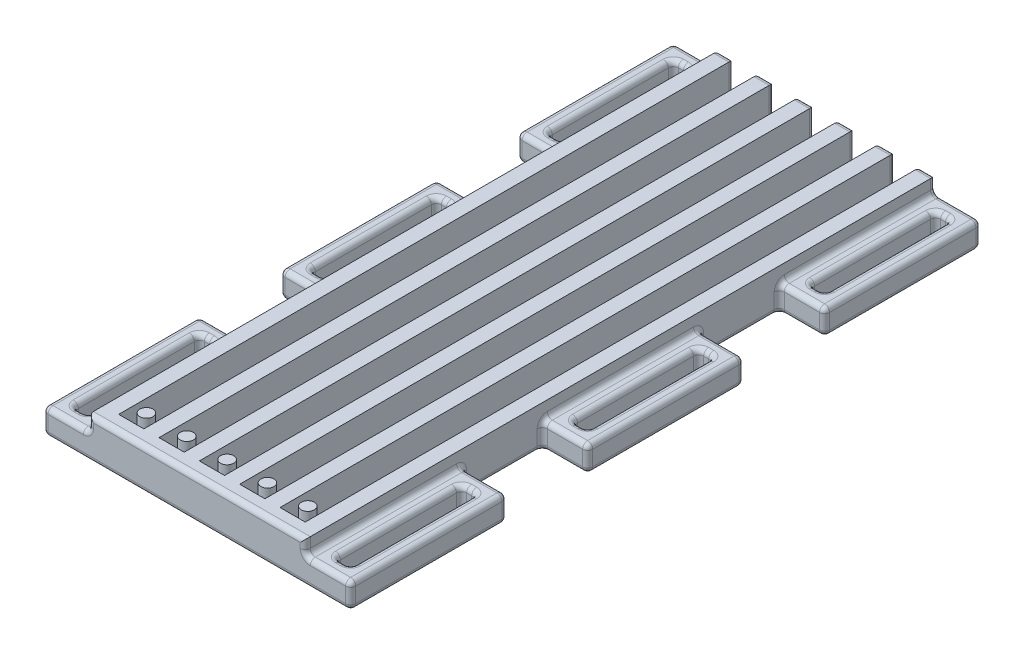
SolidWorks part; units mm, degrees
ref_plane "Front Plane" through (0, 0, 0) normal (0, 0, 1) x (1, 0, 0)
ref_plane "Top Plane" through (0, 0, 0) normal (0, 1, 0) x (1, 0, 0)
ref_plane "Right Plane" through (0, 0, 0) normal (1, 0, 0) x (0, 0, -1)
sketch "Sketch1" plane through (0, 0, 0) normal (0, 1, 0) x (1, 0, 0)
  line L1 (0, 0) -> (43, 0)
  line L2 (0, 0) -> (0, 125)
  line L3 (0, 125) -> (43, 125)
  line L4 (43, 0) -> (43, 125)
extrude "Boss-Extrude2" add sketch "Sketch1" along normal blind 8 contours L3 L4 L1 L2
sketch "Sketch2" plane through (0, 8, 0) normal (0, 1, 0) x (1, 0, 0)
  line L0 (8, 125) -> (8, 3)
  line L1 (3, 3) -> (40, 3)
  line L2 (3, 3) -> (3, 125)
  line L3 (3, 125) -> (40, 125)
  line L4 (40, 3) -> (40, 125)
  line L5 (11, 125) -> (11, 3)
  line L6 (16, 125) -> (16, 3)
  line L7 (19, 125) -> (19, 3)
  line L8 (24, 125) -> (24, 3)
  line L9 (27, 125) -> (27, 3)
  line L10 (32, 125) -> (32, 3)
  line L11 (35, 125) -> (35, 3)
  line L12 (0, 0) -> (0, 125) construction
  line L14 (0, 0) -> (43, 0) construction
  line L15 (0, 125) -> (43, 125) construction
  dimension "D1" = 3
  dimension "D2" = 3
  dimension "D3" = 3
  dimension "D4" = 3
  dimension "D5" = 5
  dimension "D6" = 5
  dimension "D7" = 5
  dimension "D8" = 5
  dimension "D9" = 5
  dimension "D10" = 3
  dimension "D11" = 3
extrude "Cut-Extrude1" cut sketch "Sketch2" against normal blind 5 contours L3 L2 L1 L0 | L6 L3 L5 L1 | L8 L3 L7 L1 | L10 L3 L9 L1 | L3 L11 L1 L4
sketch "Sketch3" plane through (0, 0, 0) normal (0, 1, 0) x (1, 0, 0)
  line L0 (0, 0) -> (0, 125) construction
  line L1 (0, 0) -> (-9, 0)
  line L2 (0, 0) -> (0, 31)
  line L3 (0, 31) -> (-9, 31)
  line L4 (-9, 0) -> (-9, 31)
  line L5 (43, 0) -> (52, 0)
  line L6 (43, 0) -> (43, 31)
  line L7 (43, 31) -> (52, 31)
  line L8 (52, 0) -> (52, 31)
  line L9 (0, 125) -> (-9, 125)
  line L10 (0, 125) -> (0, 94)
  line L11 (0, 94) -> (-9, 94)
  line L12 (-9, 125) -> (-9, 94)
  line L13 (43, 125) -> (52, 125)
  line L14 (43, 125) -> (43, 94)
  line L15 (43, 94) -> (52, 94)
  line L16 (52, 125) -> (52, 94)
  line L17 (0, 78) -> (-9, 78)
  line L18 (0, 78) -> (0, 47)
  line L19 (0, 47) -> (-9, 47)
  line L20 (-9, 78) -> (-9, 47)
  line L21 (43, 0) -> (43, 125) construction
  line L22 (43, 78) -> (52, 78)
  line L23 (43, 78) -> (43, 47)
  line L24 (43, 47) -> (52, 47)
  line L25 (52, 78) -> (52, 47)
  line L27 (-6, 28) -> (-3, 28)
  line L28 (-6, 28) -> (-6, 3)
  line L29 (-6, 3) -> (-3, 3)
  line L30 (-3, 28) -> (-3, 3)
  line L31 (46, 28) -> (49, 28)
  line L32 (46, 28) -> (46, 3)
  line L33 (46, 3) -> (49, 3)
  line L34 (49, 28) -> (49, 3)
  line L35 (46, 122) -> (49, 122)
  line L36 (46, 122) -> (46, 97)
  line L37 (46, 97) -> (49, 97)
  line L38 (49, 122) -> (49, 97)
  line L39 (46, 75) -> (49, 75)
  line L40 (46, 75) -> (46, 50)
  line L41 (46, 50) -> (49, 50)
  line L42 (49, 75) -> (49, 50)
  line L43 (-6, 75) -> (-3, 75)
  line L44 (-6, 75) -> (-6, 50)
  line L45 (-6, 50) -> (-3, 50)
  line L46 (-3, 75) -> (-3, 50)
  line L47 (-6, 122) -> (-3, 122)
  line L48 (-6, 122) -> (-6, 97)
  line L49 (-6, 97) -> (-3, 97)
  line L50 (-3, 122) -> (-3, 97)
  dimension "D1" = 25
  dimension "D2" = 25
  dimension "D3" = 3
  dimension "D4" = 3
  dimension "D5" = 3
  dimension "D6" = 3
  dimension "D7" = 3
  dimension "D8" = 3
  dimension "D9" = 3
  dimension "D10" = 3
  dimension "D11" = 3
  dimension "D12" = 3
  dimension "D13" = 3
  dimension "D14" = 3
  dimension "D15" = 25
  dimension "D16" = 3
  dimension "D17" = 3
  dimension "D18" = 3
  dimension "D19" = 3
  dimension "D20" = 3
  dimension "D21" = 3
  dimension "D22" = 3
  dimension "D23" = 25
  dimension "D24" = 3
  dimension "D25" = 25
  dimension "D26" = 3
  dimension "D27" = 3
  dimension "D28" = 3
  dimension "D29" = 3
  dimension "D30" = 3
  dimension "D31" = 3
  dimension "D32" = 3
  dimension "D33" = 3
  dimension "D34" = 3
  dimension "D35" = 3
  dimension "D36" = 25
  dimension "D37" = 16
  dimension "D38" = 16
  dimension "D39" = 16
  dimension "D40" = 16
extrude "Boss-Extrude3" add sketch "Sketch3" along normal blind 5
sketch "Sketch4" plane through (0, 3, 0) normal (0, 1, 0) x (1, 0, 0)
  line L0 (3, 3) -> (8, 3) construction
  line L1 (8, 125) -> (8, 3) construction
  line L2 (11, 125) -> (11, 3) construction
  line L3 (11, 3) -> (16, 3) construction
  line L4 (19, 3) -> (24, 3) construction
  line L5 (24, 125) -> (24, 3) construction
  line L6 (32, 125) -> (32, 3) construction
  line L7 (27, 3) -> (32, 3) construction
  line L8 (35, 3) -> (40, 3) construction
  line L9 (40, 3) -> (40, 125) construction
  circle A0 centre (5.5, 6) radius 1.3
  circle A1 centre (13.5, 6) radius 1.3
  circle A2 centre (21.5, 6) radius 1.3
  circle A3 centre (29.5, 6) radius 1.3
  circle A4 centre (37.5, 6) radius 1.3
  point P18 (21.5, 3)
  dimension "D1" = 3
  dimension "D2" = 2.5
  dimension "D3" = 2.5
  dimension "D4" = 3
  dimension "D5" = 3
  dimension "D6" = 2.5
  dimension "D7" = 2.5
  dimension "D8" = 3
  dimension "D9" = 3
  dimension "D10" = 2.5
extrude "Boss-Extrude4" add sketch "Sketch4" along normal blind 5
fillet "Fillet1" radius 1 162 edges at (47.5, 0, -94) (47.5, 5, -94) (-4.5, 0, -28) (-4.5, 5, -28) (-4.5, 0, -3) (-4.5, 5, -3) (47.5, 0, -28) (47.5, 5, -28) (47.5, 0, -3) (47.5, 5, -3) (47.5, 0, -75) (47.5, 5, -75) (47.5, 0, -50) (47.5, 5, -50) (47.5, 0, -97) (47.5, 5, -97) (47.5, 0, -122) (47.5, 5, -122) (-4.5, 0, -97) (-4.5, 5, -97) (-4.5, 0, -122) (-4.5, 5, -122) (-4.5, 0, -75) (-4.5, 5, -75) (-4.5, 0, -50) (-4.5, 5, -50) (43, 2.5, -94) (46, 2.5, -3) (46, 2.5, -28) (46, 0, -15.5) (46, 5, -15.5) (52, 0, -15.5) (52, 5, -15.5) (52, 2.5, -31) (47.5, 5, -31) (37.5, 3, -125) (35, 5.5, -125) (33.5, 8, -125) (32, 5.5, -125) (29.5, 3, -125) (27, 5.5, -125) (25.5, 8, -125) (24, 5.5, -125) (21.5, 3, -125) (19, 5.5, -125) (17.5, 8, -125) (16, 5.5, -125) (13.5, 3, -125) (11, 5.5, -125) (9.5, 8, -125) (8, 5.5, -125) (5.5, 3, -125) (3, 5.5, -125) (1.5, 8, -125) (0, 6.5, -125) (21.5, 0, -125) (43, 6.5, -125) (41.5, 8, -125) (40, 5.5, -125) (0, 2.5, -78) (-4.5, 0, -78) (-4.5, 5, -78) (21.5, 8, 0) (52, 2.5, 0) (21.5, 0, 0) (0, 2.5, -47) (-4.5, 0, -47) (-4.5, 5, -47) (-4.5, 5, -31) (-6, 2.5, -3) (-6, 2.5, -28) (-6, 0, -15.5) (-6, 5, -15.5) (-9, 2.5, -31) (-9, 2.5, 0) (-9, 0, -15.5) (-9, 5, -15.5) (-3, 2.5, -28) (-3, 2.5, -3) (-3, 0, -15.5) (-3, 5, -15.5) (49, 2.5, -28) (49, 2.5, -3) (49, 0, -15.5) (49, 5, -15.5) (43, 2.5, -47) (47.5, 0, -47) (47.5, 5, -47) (43, 2.5, -78) (47.5, 0, -78) (47.5, 5, -78) (52, 2.5, -47) (52, 2.5, -78) (52, 0, -62.5) (52, 5, -62.5) (46, 2.5, -50) (46, 2.5, -75) (46, 0, -62.5) (46, 5, -62.5) (49, 2.5, -75) (49, 2.5, -50) (49, 0, -62.5) (49, 5, -62.5) (-9, 2.5, -78) (-9, 2.5, -47) (-9, 0, -62.5) (-9, 5, -62.5) (52, 2.5, -94) (52, 2.5, -125) (52, 0, -109.5) (52, 5, -109.5) (49, 2.5, -122) (49, 2.5, -97) (49, 0, -109.5) (49, 5, -109.5) (46, 2.5, -97) (46, 2.5, -122) (46, 0, -109.5) (46, 5, -109.5) (-3, 2.5, -122) (-3, 2.5, -97) (-3, 0, -109.5) (-3, 5, -109.5) (-6, 2.5, -97) (-6, 2.5, -122) (-6, 0, -109.5) (-6, 5, -109.5) (-6, 2.5, -50) (-6, 2.5, -75) (-6, 0, -62.5) (-6, 5, -62.5) (-3, 2.5, -75) (-3, 2.5, -50) (-3, 0, -62.5) (-3, 5, -62.5) (0, 5, -62.5) (43, 5, -62.5) (47.5, 5, -125) (43, 5, -109.5) (0, 2.5, -94) (-4.5, 0, -94) (-4.5, 5, -94) (-9, 2.5, -125) (-9, 2.5, -94) (-9, 0, -109.5) (-9, 5, -109.5) (-4.5, 5, -125) (0, 5, -109.5)
